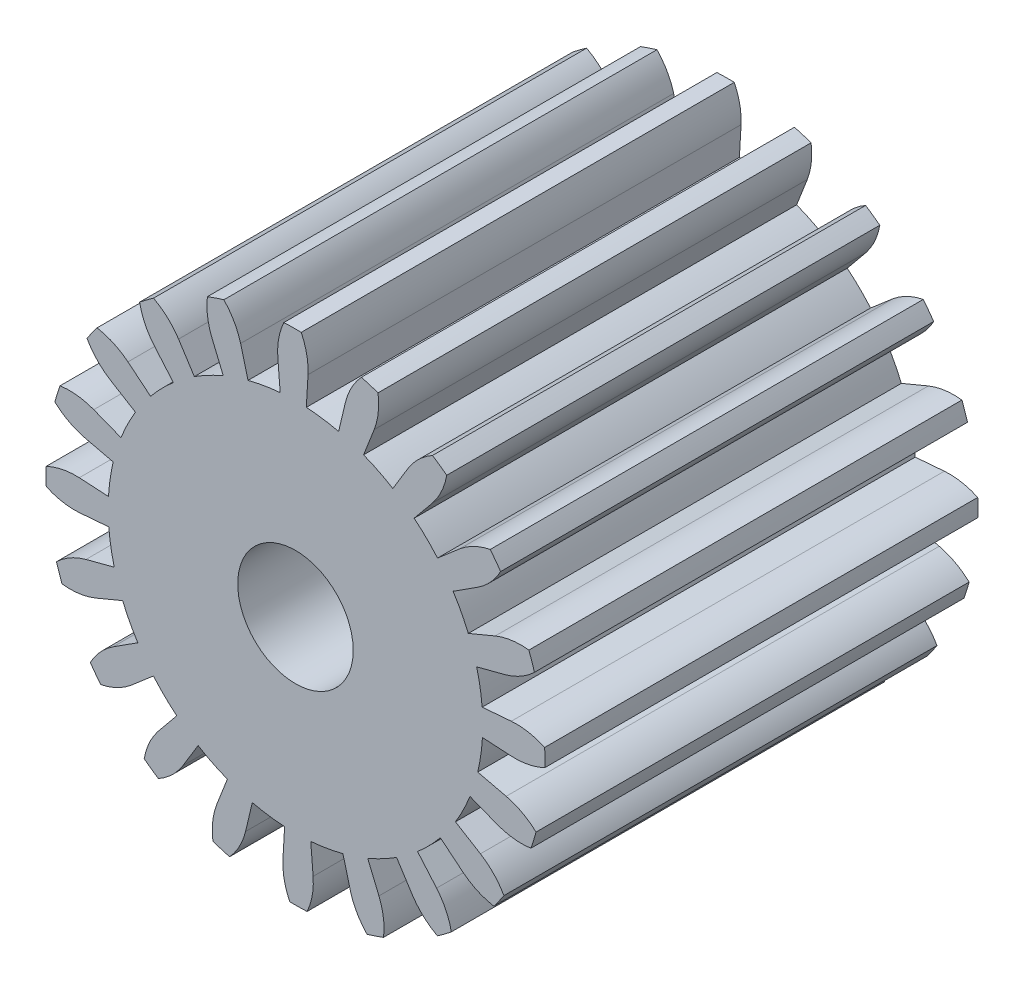
SolidWorks part; units mm, degrees
ref_plane "Front Plane" through (0, 0, 0) normal (0, 0, 1) x (1, 0, 0)
ref_plane "Top Plane" through (0, 0, 0) normal (0, 1, 0) x (1, 0, 0)
ref_plane "Right Plane" through (0, 0, 0) normal (1, 0, 0) x (0, 0, -1)
sketch "Sketch2" plane through (0, 0, 0) normal (0, 0, 1) x (1, 0, 0)
  line L0 (0, 0) -> (10.2026, 5.3514) construction
  line L1 (0, 0) -> (10.9141, 3.6894) construction
  line L2 (0, 0) -> (11.7274, 4.9003) construction
  line L3 (0, 0) -> (11.1163, 4.1955) construction
  line L4 (7.9813, 3.3349) -> (9.2269, 3.8554)
  line L5 (8.3677, 2.1917) -> (9.6737, 2.5338)
  line L6 (0, 0) -> (7.6602, 4.0179)
  line L7 (0, 0) -> (8.5269, 1.4541)
  circle A0 centre (0, 0) radius 8.65 construction
  circle A1 centre (0, 0) radius 10 construction
  circle A2 centre (0, 0) radius 11.5208 construction
  arc A3 (9.2269, 3.8554) -> (10.7787, 4.0681) centre (10.4174, 0.9363) cw
  arc A4 (7.6602, 4.0179) -> (7.9813, 3.3349) centre (0, 0) cw
  arc A5 (10.7787, 4.0681) -> (10.9141, 3.6894) centre (0, 0) cw
  arc A6 (11.0362, 3.3063) -> (10.9141, 3.6894) centre (0, 0) ccw
  arc A7 (9.6737, 2.5338) -> (11.0362, 3.3063) centre (8.8488, 5.5765) ccw
  arc A8 (8.5269, 1.4541) -> (8.3677, 2.1917) centre (0, 0) ccw
  dimension "D1" = 17.3
  dimension "D2" = 20
  dimension "D3" = 2.8708
  dimension "D4" = 9
  dimension "D5" = 4
  dimension "D6" = 2
extrude "Boss-Extrude5" add sketch "Sketch2" along normal blind 20
pattern_circular "CirPattern2" count 20 over 360 about axis through (0, 0, 0) along (0, 0, 1) of "Boss-Extrude5"
sketch "Sketch4" plane through (0, 0, 20) normal (0, 0, 1) x (1, 0, 0)
  circle A0 centre (0, 0) radius 2.667
  dimension "D1" = 5.334
extrude "Cut-Extrude1" cut sketch "Sketch4" against normal through all contours A0
